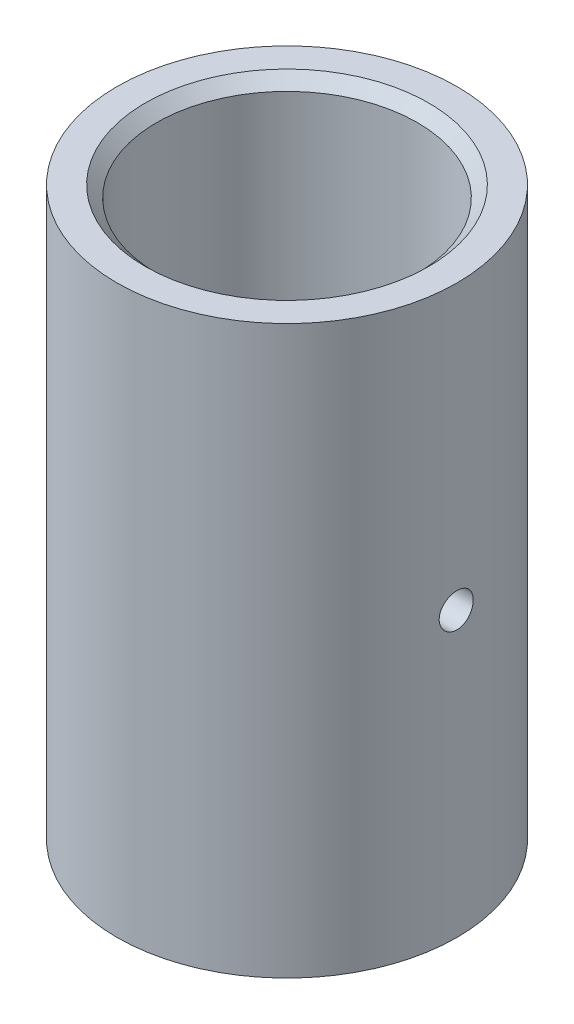
SolidWorks part; units mm, degrees
material "Silicon Rubber"
ref_plane "Front Plane" through (0, 0, 0) normal (0, 0, 1) x (1, 0, 0)
ref_plane "Top Plane" through (0, 0, 0) normal (0, 1, 0) x (1, 0, 0)
ref_plane "Right Plane" through (0, 0, 0) normal (1, 0, 0) x (0, 0, -1)
sketch "Sketch1" plane through (0, 0, 0) normal (0, 1, 0) x (1, 0, 0)
  circle A0 centre (0, 0) radius 7.5
  dimension "D1" = 15
extrude "Boss-Extrude1" add sketch "Sketch1" along normal blind 25
sketch "Sketch2" plane through (0, 25, 0) normal (0, 1, 0) x (1, 0, 0)
  circle A0 centre (0, 0) radius 5.75
  dimension "D1" = 11.5
extrude "Cut-Extrude1" cut sketch "Sketch2" against normal blind 11
chamfer "Chamfer1" distance 0.5 angle 45 1 edges at (0, 25, 5.75)
sketch "Sketch3" plane through (0, 14, 0) normal (0, 1, 0) x (1, 0, 0)
  circle A0 centre (0, 0) radius 3.5
  dimension "D1" = 7
extrude "Cut-Extrude2" cut sketch "Sketch3" against normal blind 10
sketch "Sketch4" plane through (0, 0, 0) normal (1, 0, 0) x (0, 0, -1)
  line L0 (7.5, 25) -> (-7.5, 25) construction
  line L1 (0, 0) -> (0, 27.595) construction
  circle A0 centre (0, 12.5) radius 0.75
  dimension "D2" = 1.5
  dimension "D1" = 12.5
extrude "Cut-Extrude3" cut sketch "Sketch4" against normal up to next and the other way up to next
